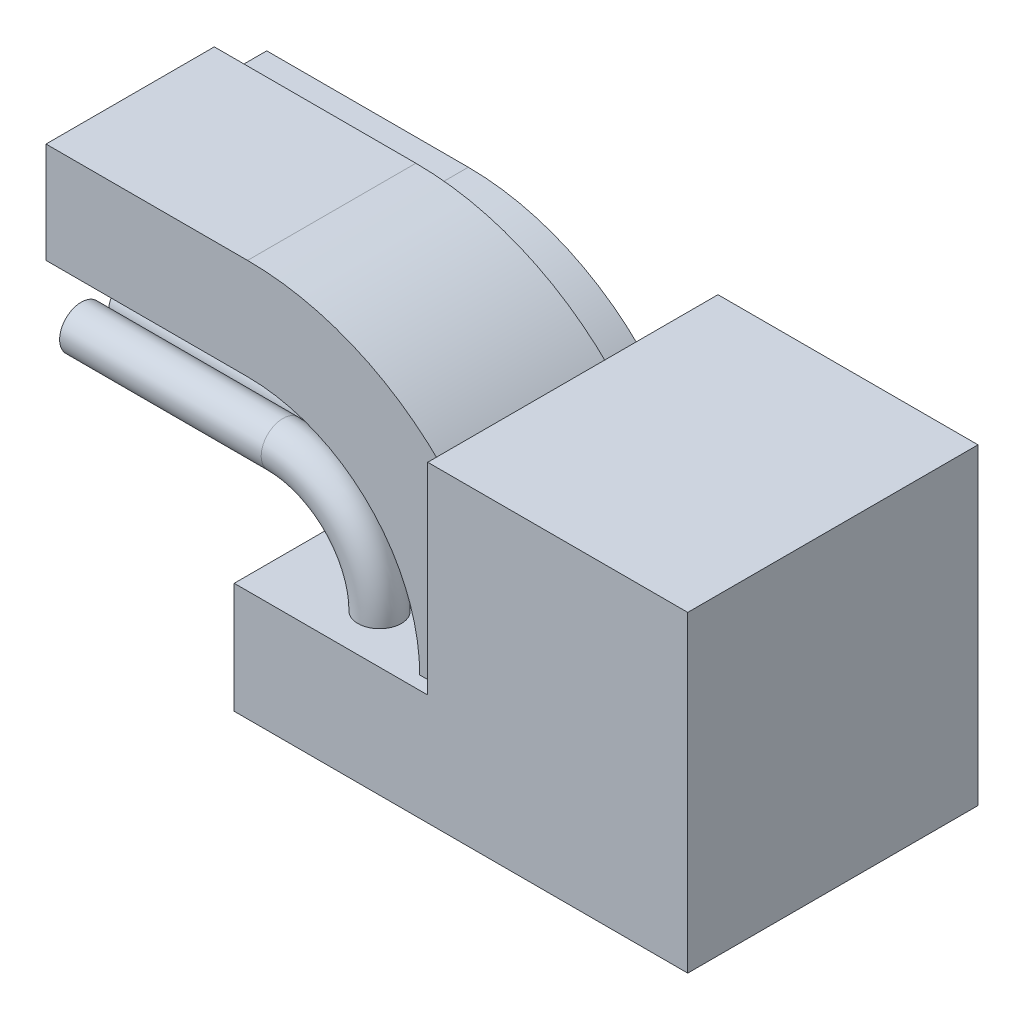
SolidWorks part; units mm, degrees
ref_plane "Front Plane" through (0, 0, 0) normal (0, 0, 1) x (1, 0, 0)
ref_plane "Top Plane" through (0, 0, 0) normal (0, 1, 0) x (1, 0, 0)
ref_plane "Right Plane" through (0, 0, 0) normal (1, 0, 0) x (0, 0, -1)
sketch "Sketch1" plane through (0, 0, 0) normal (0, 1, 0) x (1, 0, 0)
  line L1 (-28.575, -18.288) -> (28.575, -18.288)
  line L2 (-28.575, -18.288) -> (-28.575, 18.288)
  line L3 (-28.575, 18.288) -> (28.575, 18.288)
  line L4 (28.575, -18.288) -> (28.575, 18.288)
  line L5 (-28.575, -18.288) -> (28.575, 18.288) construction
  line L6 (-28.575, 18.288) -> (28.575, -18.288) construction
  point P0 (0, 0)
  dimension "D1" = 57.15
  dimension "D2" = 36.576
extrude "Boss-Extrude1" add sketch "Sketch1" along normal blind 13.97
sketch "Sketch2" plane through (0, 13.97, 0) normal (0, 1, 0) x (1, 0, 0)
  line L0 (-28.575, -18.288) -> (28.575, -18.288) construction
  line L1 (28.575, 18.288) -> (-4.191, 18.288)
  line L2 (28.575, 18.288) -> (28.575, -18.288)
  line L3 (28.575, -18.288) -> (-4.191, -18.288)
  line L4 (-4.191, 18.288) -> (-4.191, -18.288)
  dimension "D1" = 32.766
extrude "Boss-Extrude2" add sketch "Sketch2" along normal blind 25.4
sketch "Sketch4" plane through (0, 13.97, 0) normal (0, 1, 0) x (1, 0, 0)
  line L0 (-16.383, -18.288) -> (-16.383, 18.288) construction
  line L1 (-28.575, -18.288) -> (-4.191, -18.288) construction
  line L2 (-4.191, 18.288) -> (-28.575, 18.288) construction
  line L3 (-28.575, -18.288) -> (-28.575, 18.288) construction
  line L4 (5.8192, -16.6036) -> (-6.8808, -16.6036)
  line L5 (5.8192, -16.6036) -> (5.8192, 4.6054)
  line L6 (5.8192, 4.6054) -> (2.0827, 4.6054)
  line L7 (-6.8808, -16.6036) -> (-6.8808, 4.6054)
  line L8 (-16.383, -5.9991) -> (-6.8808, -5.9991) construction
  line L9 (-0.9653, 4.6054) -> (-6.8808, 4.6054)
  line L11 (2.0827, 4.6054) -> (2.0827, 11.2094)
  line L12 (2.0827, 11.2094) -> (-0.9653, 11.2094)
  line L13 (-0.9653, 4.6054) -> (-0.9653, 11.2094)
  circle A0 centre (-16.383, 0) radius 2.7305
  circle A1 centre (-16.383, -5.9991) radius 2.7305
  circle A2 centre (-16.383, -12.157) radius 2.7305
  dimension "D1" = 5.461
  dimension "D2" = 5.461
  dimension "D3" = 5.461
  dimension "D4" = 12.7
  dimension "D5" = 21.209
  dimension "D6" = 6.604
  dimension "D7" = 3.048
revolve "Revolve1" add sketch "Sketch4" angle 90 about L3
sketch "Sketch5" plane through (-28.575, 0, 0) normal (-1, 0, 0) x (0, -1, 0)
  line L0 (-44.6277, -4.6054) -> (-48.3642, -4.6054)
  line L1 (-35.6642, -4.6054) -> (-41.5797, -4.6054)
  line L2 (-35.6642, -4.6054) -> (-35.6642, 16.6036)
  line L3 (-35.6642, 16.6036) -> (-48.3642, 16.6036)
  line L4 (-48.3642, -4.6054) -> (-48.3642, 16.6036)
  line L6 (-44.6277, -11.2094) -> (-41.5797, -11.2094)
  line L7 (-44.6277, -11.2094) -> (-44.6277, -4.6054)
  line L9 (-41.5797, -11.2094) -> (-41.5797, -4.6054)
extrude "Boss-Extrude4" add sketch "Sketch5" along normal blind 25.4
sketch "Sketch6" plane through (-28.575, 0, 0) normal (-1, 0, 0) x (0, -1, 0)
  circle A0 centre (-26.162, 0) radius 2.7305
  circle A1 centre (-26.162, 0) radius 2.7305 construction
  point P0 (-26.162, 2.7305)
  point P3 (-26.162, 2.7305)
  point P6 (-26.162, 2.7305)
  point P7 (-26.405, -2.7197)
extrude "Boss-Extrude5" add sketch "Sketch6" along normal blind 25.4
sketch "Sketch7" plane through (-28.575, 0, 0) normal (-1, 0, 0) x (0, -1, 0)
  circle A0 centre (-26.162, 5.9991) radius 2.7305
  circle A1 centre (-26.162, 5.9991) radius 2.7305 construction
  point P0 (-26.162, 8.7296)
  point P3 (-27.9293, 3.9177)
  point P5 (-27.9293, 3.9177)
  point P8 (-27.0646, 3.4221)
  point P9 (-24.8654, 3.5961)
extrude "Boss-Extrude6" add sketch "Sketch7" along normal blind 25.4
sketch "Sketch8" plane through (-28.575, 0, 0) normal (-1, 0, 0) x (0, -1, 0)
  circle A0 centre (-26.162, 12.157) radius 2.7305
  circle A1 centre (-26.162, 12.157) radius 2.7305 construction
  point P0 (-27.9193, 10.0672)
  point P3 (-27.9193, 10.0672)
  point P6 (-24.3828, 10.0858)
  point P7 (-26.9566, 9.5447)
extrude "Boss-Extrude7" add sketch "Sketch8" along normal blind 25.4
equation "\"Wire Size\"= 0.215"
equation "\"D1@Sketch4\"=\"Wire Size\""
equation "\"D2@Sketch4\"= \"Wire Size\""
equation "\"D3@Sketch4\"= \"Wire Size\""
equation "\"Deans Width\"= 0.5"
equation "\"D4@Sketch4\"=\"Deans Width\""
equation "\"Deans Length\"= 0.835"
equation "\"D5@Sketch4\"=\"Deans Length\""
